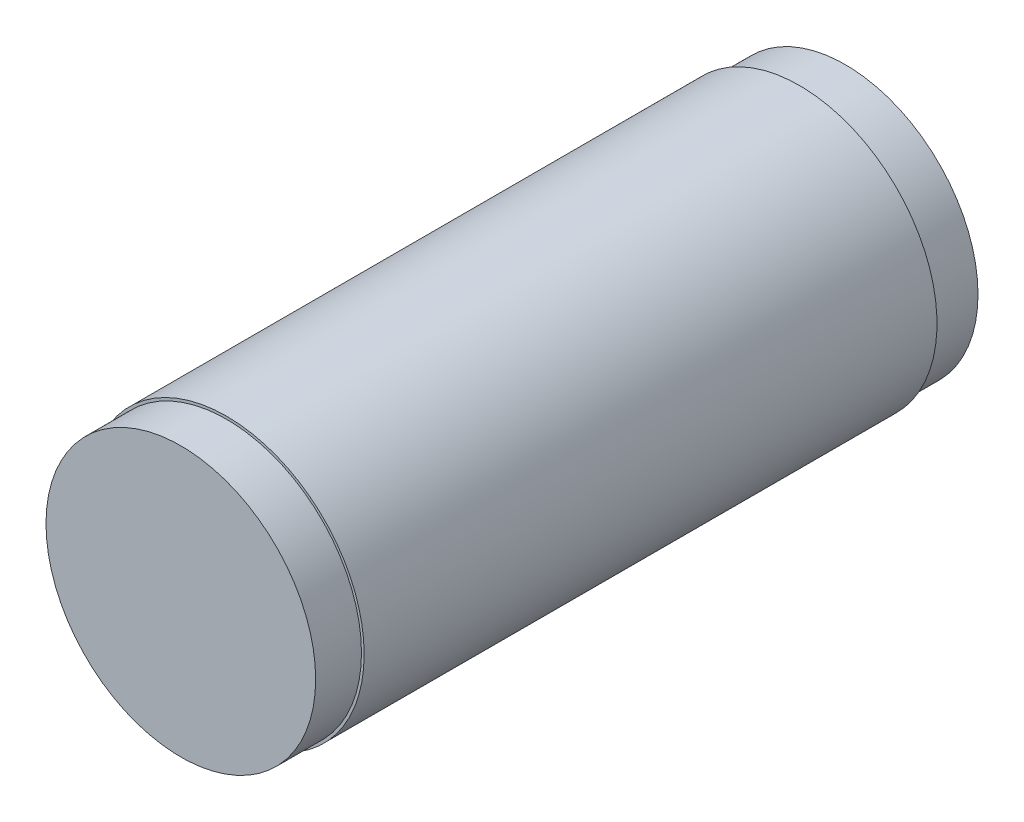
SolidWorks part; units mm, degrees
material "Ti-6Al-2Sn-2Zr-2Mo-2Cr-0.25Si (SS)"
ref_plane "Front Plane" through (0, 0, 0) normal (0, 0, 1) x (1, 0, 0)
ref_plane "Top Plane" through (0, 0, 0) normal (0, 1, 0) x (1, 0, 0)
ref_plane "Right Plane" through (0, 0, 0) normal (1, 0, 0) x (0, 0, -1)
sketch "Sketch1" plane through (0, 0, 0) normal (0, 0, 1) x (1, 0, 0)
  circle A0 centre (0, 0) radius 25
  circle A1 centre (0, 0) radius 30
  dimension "D1" = 50
  dimension "D2" = 60
extrude "Boss-Extrude1" add sketch "Sketch1" along normal blind 145
sketch "Sketch2" plane through (0, 0, 0) normal (0, 0, 1) x (1, 0, 0)
  circle A1 centre (0, 0) radius 25
  dimension "D2" = 50
extrude "Boss-Extrude2" add sketch "Sketch2" along normal blind 10
ref_plane "Plane1" through (0, 0, 135) normal (0, 0, 1) x (1, 0, 0)
sketch "Sketch3" plane through (0, 0, 135) normal (0, 0, 1) x (1, 0, 0)
  circle A0 centre (0, 0) radius 25
  dimension "D1" = 50
extrude "Boss-Extrude3" add sketch "Sketch3" along normal blind 10
sketch "Sketch11" plane through (0, 0, 0) normal (0, 0, -1) x (-1, 0, 0)
  circle A0 centre (0, 0) radius 28.946
  circle A1 centre (0, 0) radius 30
extrude "Cut-Extrude2" cut sketch "Sketch11" against normal blind 10
sketch "Sketch12" plane through (0, 0, 145) normal (0, 0, 1) x (1, 0, 0)
  circle A0 centre (0, 0) radius 30
  circle A1 centre (0, 0) radius 29.421
extrude "Cut-Extrude3" cut sketch "Sketch12" against normal blind 10
ref_plane "Plane4" through (0, 0, 145) normal (0, 0, 1) x (1, 0, 0)
